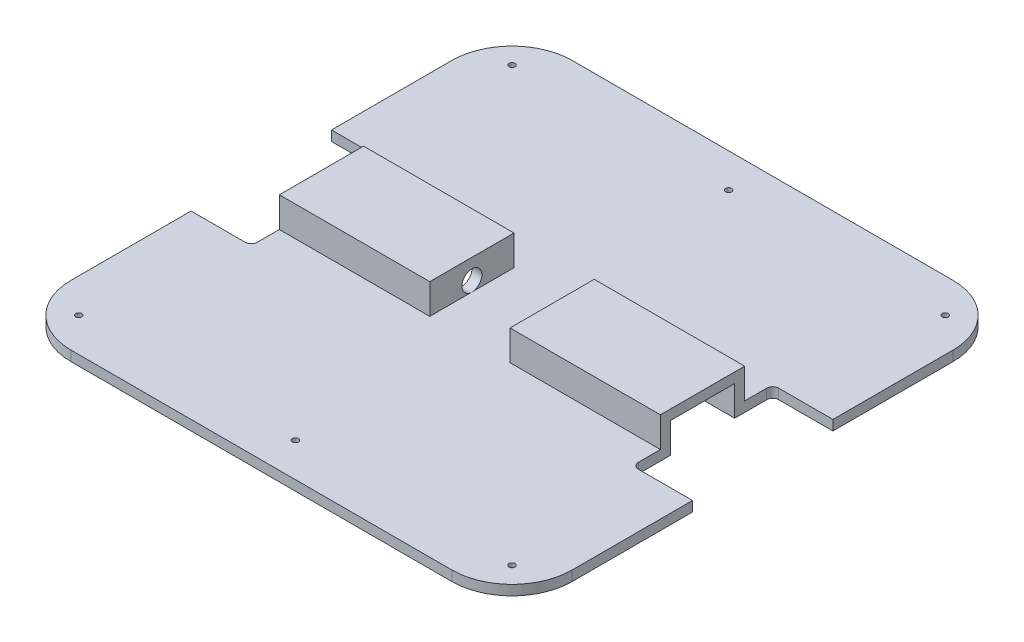
SolidWorks part; units mm, degrees
ref_plane "Front Plane" through (0, 0, 0) normal (0, 0, 1) x (1, 0, 0)
ref_plane "Top Plane" through (0, 0, 0) normal (0, 1, 0) x (1, 0, 0)
ref_plane "Right Plane" through (0, 0, 0) normal (1, 0, 0) x (0, 0, -1)
sketch "Sketch3" plane through (0, 0, 0) normal (1, 0, 0) x (0, 0, -1)
  line L0 (0, 0) -> (0, 5)
  line L1 (0, 5) -> (104, 5)
  line L2 (104, 5) -> (104, 20)
  line L3 (104, 20) -> (146, 20)
  line L4 (146, 20) -> (146, 5)
  line L5 (146, 5) -> (250, 5)
  line L6 (250, 5) -> (250, 0)
  line L7 (250, 0) -> (0, 0)
  point P3 (0, 0)
  dimension "D1" = 250
  dimension "D2" = 5
  dimension "D3" = 42
  dimension "D4" = 20
  dimension "D5" = 104
  dimension "D6" = 104
extrude "Boss-Extrude1" add sketch "Sketch3" along normal mid plane 250
sketch "Sketch4" plane through (125, 0, 0) normal (1, 0, 0) x (0, 0, -1)
  line L0 (109, 0) -> (109, 15)
  line L1 (0, 0) -> (250, 0) construction
  line L2 (109, 15) -> (141, 15)
  line L3 (141, 15) -> (141, 0)
  line L4 (141, 0) -> (109, 0)
  line L5 (146, 5) -> (146, 20) construction
  line L6 (104, 20) -> (104, 5) construction
  line L7 (146, 20) -> (104, 20) construction
  dimension "D1" = 5
  dimension "D2" = 5
  dimension "D3" = 5
extrude "Cut-Extrude1" cut sketch "Sketch4" against normal blind 100
sketch "Sketch5" plane through (-125, 0, 0) normal (-1, 0, 0) x (0, 0, 1)
  line L0 (-141, 0) -> (-141, 15)
  line L1 (-141, 15) -> (-109, 15)
  line L2 (-109, 15) -> (-109, 0)
  line L3 (-109, 0) -> (-141, 0)
  line L4 (-146, 5) -> (-146, 20) construction
  line L6 (-104, 20) -> (-104, 5) construction
  line L7 (-146, 20) -> (-104, 20) construction
  dimension "D1" = 5
  dimension "D2" = 5
  dimension "D3" = 5
extrude "Cut-Extrude2" cut sketch "Sketch5" against normal blind 100
sketch "Sketch6" plane through (0, 20, 0) normal (0, 1, 0) x (1, 0, 0)
  line L0 (-125, 125) -> (125, 125) construction
  line L1 (-125, 146) -> (-125, 104) construction
  line L2 (125, 146) -> (125, 104) construction
  line L3 (-125, 90) -> (-125, 160)
  line L4 (-125, 250) -> (-125, 146) construction
  line L5 (-125, 160) -> (-95, 160)
  line L6 (-95, 160) -> (-95, 90)
  line L8 (-125, 90) -> (-95, 90)
  line L9 (0, 0) -> (0, 250) construction
  line L10 (125, 0) -> (-125, 0) construction
  line L11 (125, 250) -> (-125, 250) construction
  line L12 (95, 160) -> (95, 90)
  line L13 (125, 90) -> (125, 160)
  line L14 (125, 90) -> (95, 90)
  line L15 (125, 160) -> (95, 160)
  dimension "D2" = 30
extrude "Cut-Extrude3" cut sketch "Sketch6" against normal up to next
sketch "Sketch7" plane through (0, 20, 0) normal (0, 1, 0) x (1, 0, 0)
  line L0 (0, 0) -> (0, 250) construction
  line L1 (125, 250) -> (-125, 250) construction
  line L2 (0, 146) -> (-20, 146)
  line L3 (95, 146) -> (-95, 146) construction
  line L4 (95, 146) -> (-95, 146) construction
  line L5 (-20, 146) -> (-20, 104)
  line L6 (95, 104) -> (-95, 104) construction
  line L7 (-20, 104) -> (0, 104)
  line L8 (0, 146) -> (20, 146)
  line L9 (20, 146) -> (20, 104)
  line L10 (20, 104) -> (0, 104)
  dimension "D1" = 20
extrude "Cut-Extrude4" cut sketch "Sketch7" against normal blind 15
sketch "Sketch8" plane through (20, 0, 0) normal (-1, 0, 0) x (0, 0, 1)
  line L0 (-125, 20) -> (-125, 0) construction
  line L1 (-104, 20) -> (-146, 20) construction
  line L2 (-141, 0) -> (-109, 0) construction
  line L3 (-109, 15) -> (-141, 15) construction
  line L4 (-146, 5) -> (-160, 5) construction
  line L5 (-141, 10) -> (-109, 10) construction
  line L6 (-141, 15) -> (-141, 0) construction
  line L7 (-109, 15) -> (-109, 0) construction
  circle A0 centre (-125, 10) radius 4.5
  dimension "D1" = 9
  dimension "D2" = 10
  dimension "D3" = 5
extrude "Cut-Extrude5" cut sketch "Sketch8" against normal blind 15
sketch "Sketch9" plane through (-20, 0, 0) normal (1, 0, 0) x (0, 0, -1)
  circle A0 centre (125, 10) radius 5
  point P3 (0, 0)
  dimension "D1" = 10
extrude "Cut-Extrude6" cut sketch "Sketch9" against normal blind 15
fillet "Fillet1" radius 3 4 edges at (-95, 2.5, -90) (-95, 2.5, -160) (95, 2.5, -160) (95, 2.5, -90)
fillet "Fillet2" radius 30 4 edges at (125, 2.5, 0) (-125, 2.5, 0) (-125, 2.5, -250) (125, 2.5, -250)
sketch "Sketch11" plane through (0, 5, 0) normal (0, 1, 0) x (1, 0, 0)
  line L0 (0, 0) -> (0, 250) construction
  line L1 (95, 250) -> (-95, 250) construction
  line L2 (0, 125) -> (130.5078, 125) construction
  line L3 (130.5078, 125) -> (-126.1576, 125) construction
  line L4 (-108, 17) -> (108, 17) construction
  line L5 (-108, 233) -> (108, 233) construction
  circle A0 centre (-108, 233) radius 1.5
  circle A1 centre (108, 233) radius 1.5
  circle A2 centre (108, 17) radius 1.5
  circle A3 centre (-108, 17) radius 1.5
  circle A4 centre (0, 17) radius 1.5
  circle A5 centre (0, 233) radius 1.5022
  point P20 (0, 17)
  dimension "D1" = 3
  dimension "D3" = 3.0044
  dimension "D2" = 108
extrude "Cut-Extrude7" cut sketch "Sketch11" against normal up to next
